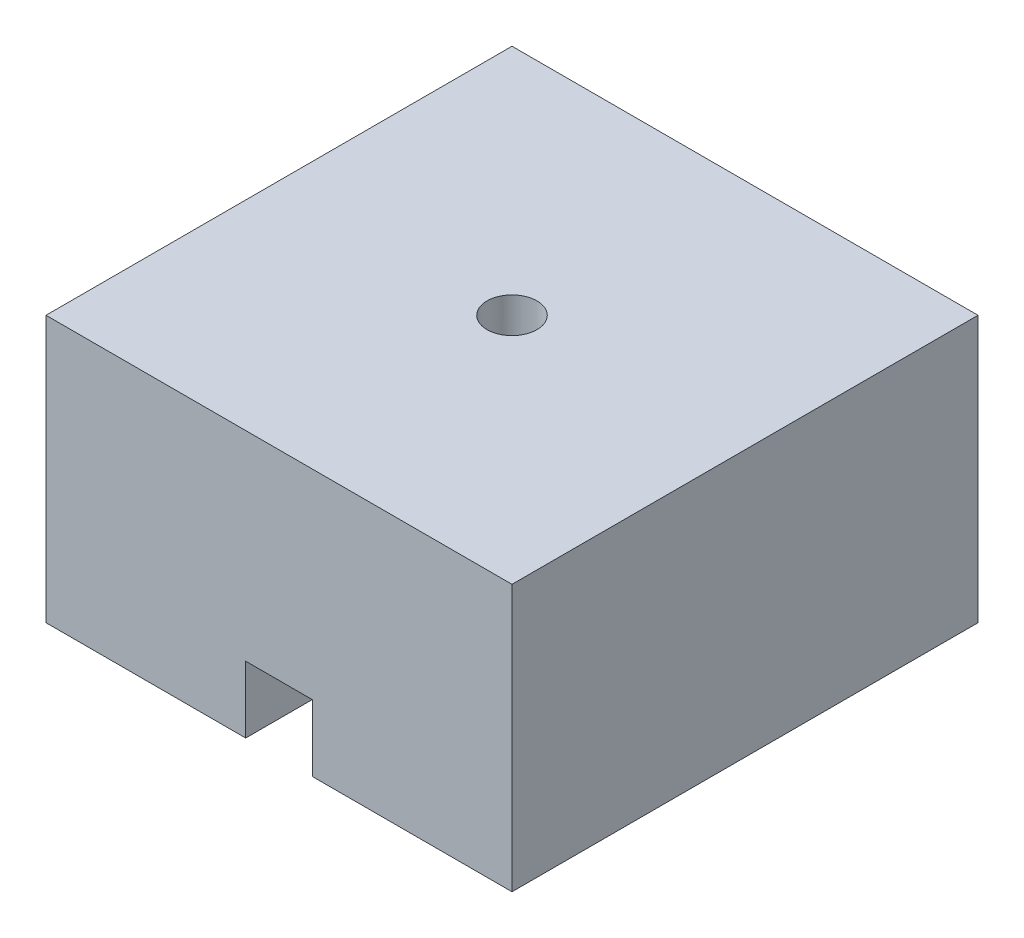
SolidWorks part; units mm, degrees
ref_plane "Front Plane" through (0, 0, 0) normal (0, 0, 1) x (1, 0, 0)
ref_plane "Top Plane" through (0, 0, 0) normal (0, 1, 0) x (1, 0, 0)
ref_plane "Right Plane" through (0, 0, 0) normal (1, 0, 0) x (0, 0, -1)
sketch "Sketch1" plane through (0, 0, 0) normal (0, 1, 0) x (1, 0, 0)
  line L1 (-44.45, 44.45) -> (44.45, 44.45)
  line L2 (-44.45, 44.45) -> (-44.45, -44.45)
  line L3 (-44.45, -44.45) -> (44.45, -44.45)
  line L4 (44.45, 44.45) -> (44.45, -44.45)
  line L5 (-44.45, 44.45) -> (44.45, -44.45) construction
  line L6 (-44.45, -44.45) -> (44.45, 44.45) construction
  point P0 (0, 0)
  dimension "D1" = 88.9
  dimension "D2" = 88.9
extrude "Boss-Extrude1" add sketch "Sketch1" along normal blind 50.8
shell "Shell1" thickness 1.5875
sketch "Sketch4" plane through (0, 50.8, 0) normal (0, 1, 0) x (1, 0, 0)
  circle A0 centre (0, 0) radius 4.7625
  dimension "D1" = 9.525
extrude "Cut-Extrude3" cut sketch "Sketch4" against normal through all
sketch "Sketch5" plane through (0, 49.2125, 0) normal (0, -1, 0) x (1, 0, 0)
  line L1 (-6.35, 34.925) -> (6.35, 34.925)
  line L2 (-6.35, 34.925) -> (-6.35, -34.925)
  line L3 (-6.35, -34.925) -> (6.35, -34.925)
  line L4 (6.35, 34.925) -> (6.35, -34.925)
  line L5 (-6.35, 34.925) -> (6.35, -34.925) construction
  line L6 (-6.35, -34.925) -> (6.35, 34.925) construction
  point P0 (0, 0)
  dimension "D1" = 12.7
  dimension "D2" = 69.85
extrude "Extrude-Thin1" add sketch "Sketch5" along normal up to surface (49.2125 mm away) thin up to face at (0, 0, 0) thin type one direction wall 1.5875
sketch "Sketch10" plane through (0, 49.2125, 0) normal (0, -1, 0) x (1, 0, 0)
  circle A0 centre (0, 0) radius 4.7625 construction
  circle A1 centre (0, 0) radius 4.7625
  circle A2 centre (0, 0) radius 7.9375
  dimension "D1" = 3.175
extrude "Boss-Extrude5" add sketch "Sketch10" along normal blind 6.35
sketch "Sketch14" plane through (0, 0, 44.45) normal (0, 0, 1) x (1, 0, 0)
  line L0 (-44.45, 0) -> (44.45, 0) construction
  line L1 (7.9375, 0) -> (-7.9375, 0)
  line L2 (7.9375, 0) -> (7.9375, 14.2875)
  line L3 (7.9375, 14.2875) -> (-7.9375, 14.2875)
  line L4 (-7.9375, 0) -> (-7.9375, 14.2875)
  point P6 (0, 14.2875)
  dimension "D1" = 15.875
  dimension "D2" = 14.2875
extrude "Boss-Extrude7" add sketch "Sketch14" against normal up to surface (7.9375 mm away) up to face at (0, 24.6062, 36.5125)
sketch "Sketch15" plane through (0, 0, 44.45) normal (0, 0, 1) x (1, 0, 0)
  line L0 (-44.45, 0) -> (44.45, 0) construction
  line L1 (6.35, 0) -> (-6.35, 0)
  line L2 (6.35, 0) -> (6.35, 12.7)
  line L3 (6.35, 12.7) -> (-6.35, 12.7)
  line L4 (-6.35, 0) -> (-6.35, 12.7)
  point P6 (0, 12.7)
  dimension "D1" = 12.7
  dimension "D2" = 12.7
extrude "Cut-Extrude6" cut sketch "Sketch15" against normal up to vertex
